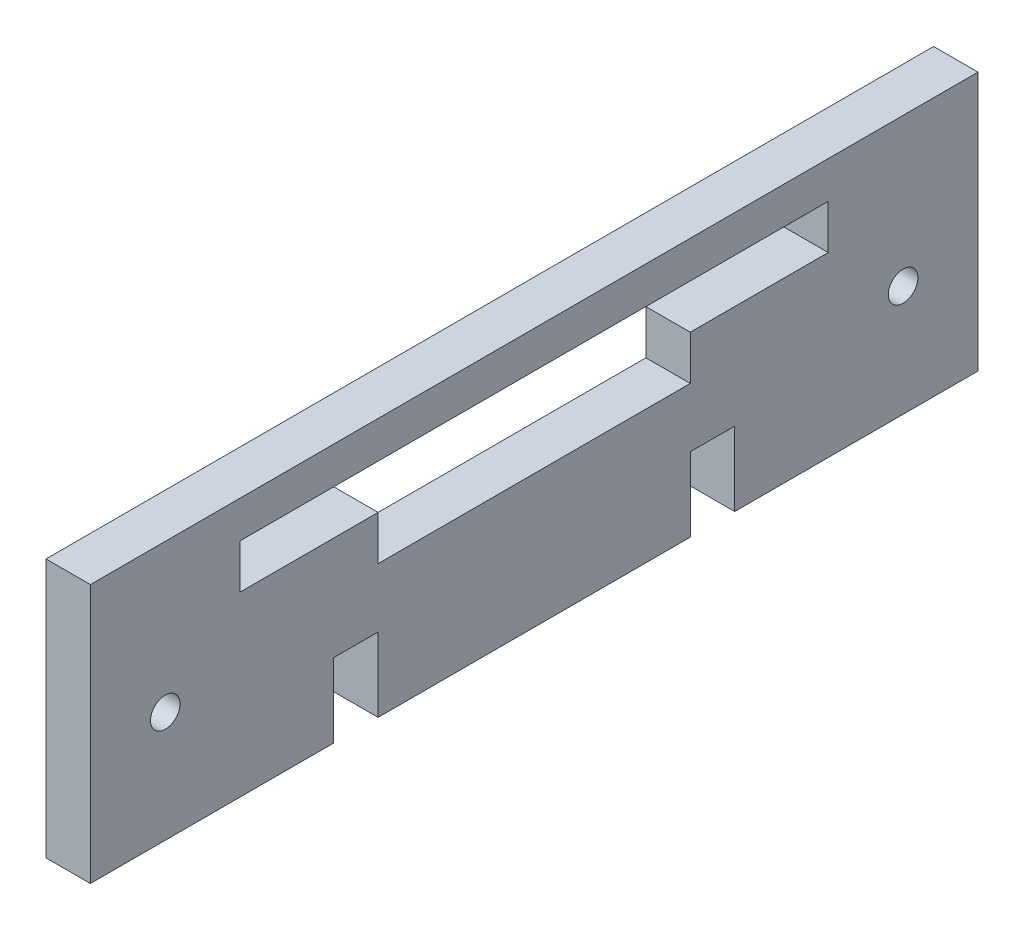
SolidWorks part; units mm, degrees
ref_plane "Front Plane" through (0, 0, 0) normal (0, 0, 1) x (1, 0, 0)
ref_plane "Top Plane" through (0, 0, 0) normal (0, 1, 0) x (1, 0, 0)
ref_plane "Right Plane" through (0, 0, 0) normal (1, 0, 0) x (0, 0, -1)
sketch "Sketch1" plane through (0, 0, 0) normal (1, 0, 0) x (0, 0, -1)
  line L0 (39.75, 15) -> (39.75, 9)
  line L1 (-60, 15) -> (-39.75, 15)
  line L2 (-60, 15) -> (-60, -15)
  line L3 (-60, -15) -> (60, -15)
  line L4 (60, 15) -> (60, -15)
  line L5 (-60, 15) -> (60, -15) construction
  line L6 (-60, -15) -> (60, 15) construction
  line L8 (-39.75, 15) -> (-39.75, 9)
  line L9 (-39.75, 9) -> (39.75, 9)
  line L11 (39.75, 15) -> (60, 15)
  point P0 (0, 0)
  dimension "D1" = 120
  dimension "D2" = 30
  dimension "D3" = 79.5
  dimension "D4" = 6
extrude "Boss-Extrude1" add sketch "Sketch1" along normal blind 6
sketch "Sketch2" plane through (6, 0, 0) normal (1, 0, 0) x (0, 0, -1)
  line L1 (-60, 15) -> (-60, -15) construction
  line L2 (-39.75, 15) -> (-60, 15) construction
  line L3 (0, 0) -> (0, -11.1697) construction
  circle A0 centre (-49.875, 0) radius 2
  circle A1 centre (49.875, 0) radius 2
  point P6 (-60, 0)
  point P7 (-49.875, 15)
  dimension "D1" = 4
extrude "Cut-Extrude1" cut sketch "Sketch2" against normal blind 10
sketch "Sketch3" plane through (0, 15, 0) normal (0, 1, 0) x (1, 0, 0)
  line L1 (0, -60) -> (6, -60)
  line L2 (0, -60) -> (0, 60)
  line L3 (0, 60) -> (6, 60)
  line L4 (6, -60) -> (6, 60)
extrude "Boss-Extrude2" add sketch "Sketch3" along normal blind 5
sketch "Sketch4" plane through (6, 0, 0) normal (1, 0, 0) x (0, 0, -1)
  line L0 (-60, -15) -> (60, -15) construction
  line L1 (-27.1, -15) -> (-21.1, -15)
  line L2 (-27.1, -15) -> (-27.1, -5)
  line L3 (-27.1, -5) -> (-21.1, -5)
  line L4 (-21.1, -15) -> (-21.1, -5)
  line L5 (-21.1, -5) -> (21.1, -5) construction
  line L6 (21.1, -15) -> (27.1, -15)
  line L7 (21.1, -15) -> (21.1, -5)
  line L8 (21.1, -5) -> (27.1, -5)
  line L9 (27.1, -15) -> (27.1, -5)
  point P10 (0, -5)
  dimension "D1" = 6
  dimension "D2" = 10
  dimension "D3" = 42.2
extrude "Cut-Extrude2" cut sketch "Sketch4" against normal up to vertex (6 mm away) up to point (0, 0, 0)
sketch "Sketch5" plane through (6, 0, 0) normal (1, 0, 0) x (0, 0, -1)
  line L0 (39.75, 9) -> (-39.75, 9) construction
  line L1 (-21.1, 9) -> (21.1, 9)
  line L2 (-21.1, 9) -> (-21.1, 3)
  line L3 (-21.1, 3) -> (21.1, 3)
  line L4 (21.1, 9) -> (21.1, 3)
  line L5 (-21.1, -15) -> (-21.1, -5) construction
  line L6 (21.1, -5) -> (21.1, -15) construction
  dimension "D1" = 6
extrude "Cut-Extrude3" cut sketch "Sketch5" against normal through all contours L2 L1 L4 L3
